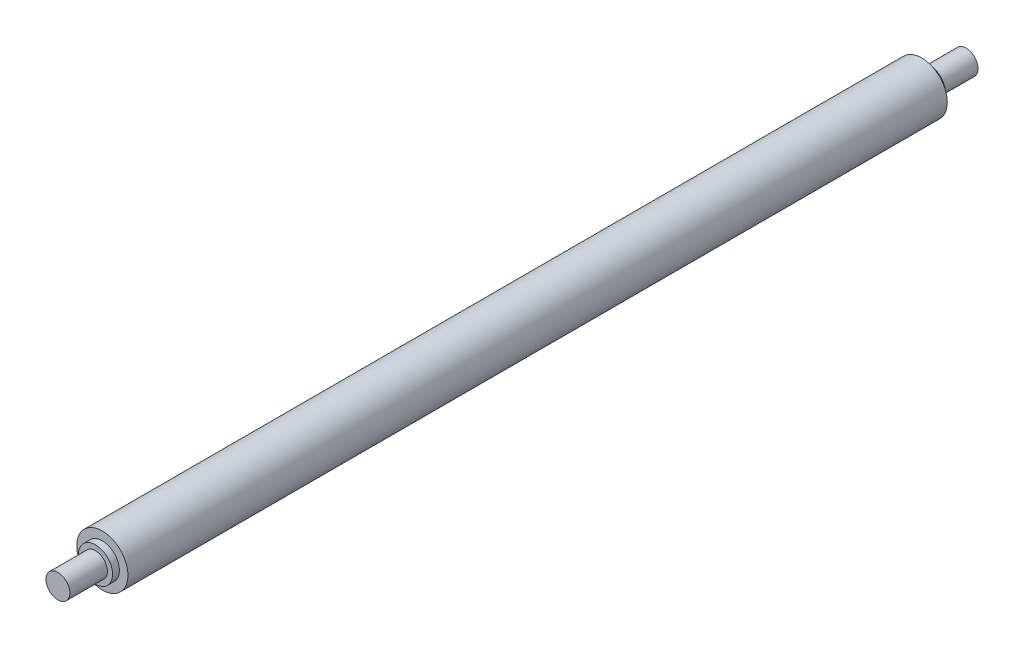
SolidWorks part; units mm, degrees
ref_plane "前视基准面" through (0, 0, 0) normal (0, 0, 1) x (1, 0, 0)
ref_plane "上视基准面" through (0, 0, 0) normal (0, 1, 0) x (1, 0, 0)
ref_plane "右视基准面" through (0, 0, 0) normal (1, 0, 0) x (0, 0, -1)
sketch "草图1" plane through (0, 0, 0) normal (0, 0, 1) x (1, 0, 0)
  circle A0 centre (0, 0) radius 7.5
  dimension "D1" = 15
extrude "凸台-拉伸1" add sketch "草图1" along normal blind 240
sketch "草图2" plane through (0, 0, 0) normal (0, 0, -1) x (-1, 0, 0)
  circle A0 centre (0, 0) radius 3.5
  dimension "D1" = 7
extrude "凸台-拉伸2" add sketch "草图2" along normal blind 13
sketch "草图3" plane through (0, 0, 240) normal (0, 0, 1) x (1, 0, 0)
  circle A0 centre (0, 0) radius 3.5
  dimension "D1" = 7
extrude "凸台-拉伸3" add sketch "草图3" along normal blind 13
sketch "草图4" plane through (0, 0, 0) normal (0, 0, -1) x (-1, 0, 0)
  circle A0 centre (0, 0) radius 5
  dimension "D1" = 10
extrude "凸台-拉伸4" add sketch "草图4" along normal blind 2
sketch "草图5" plane through (0, 0, 240) normal (0, 0, 1) x (1, 0, 0)
  circle A0 centre (0, 0) radius 5
  dimension "D1" = 10
extrude "凸台-拉伸5" add sketch "草图5" along normal blind 2
